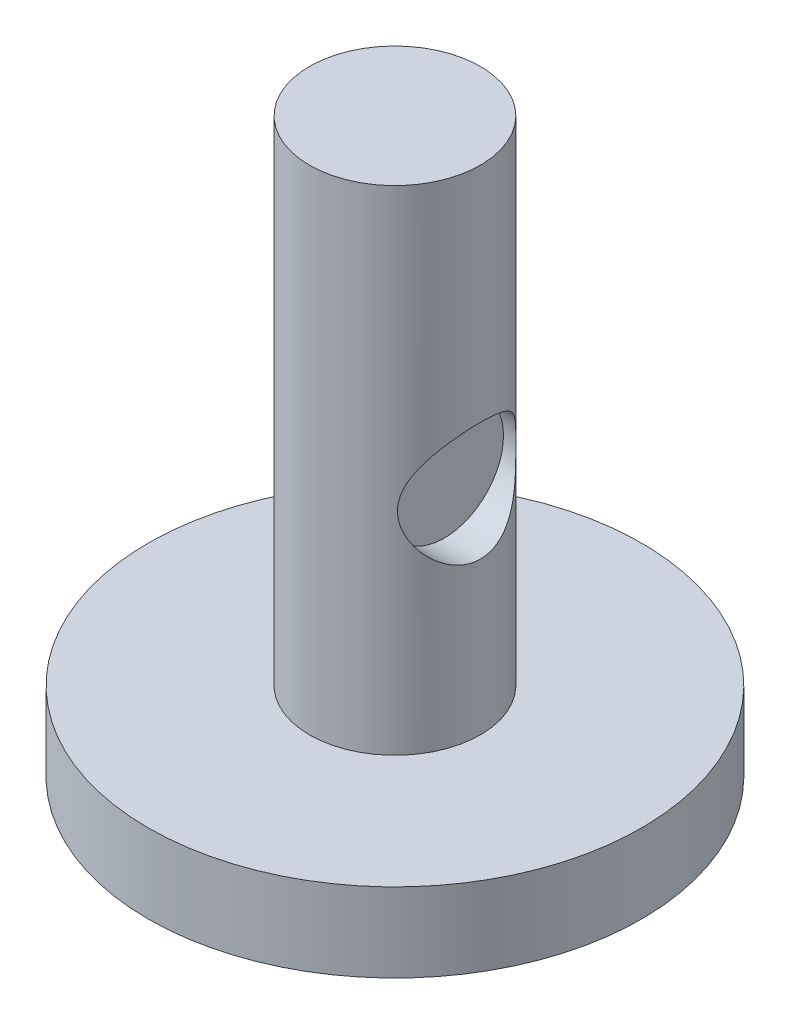
SolidWorks part; units mm, degrees
ref_plane "Front Plane" through (0, 0, 0) normal (0, 0, 1) x (1, 0, 0)
ref_plane "Top Plane" through (0, 0, 0) normal (0, 1, 0) x (1, 0, 0)
ref_plane "Right Plane" through (0, 0, 0) normal (1, 0, 0) x (0, 0, -1)
sketch "Sketch1" plane through (0, 0, 0) normal (0, 1, 0) x (1, 0, 0)
  circle A0 centre (0, 0) radius 25
  dimension "D1" = 50
extrude "Boss-Extrude1" add sketch "Sketch1" along normal blind 8
sketch "Sketch2" plane through (0, 8, 0) normal (0, 1, 0) x (1, 0, 0)
  circle A0 centre (0, 0) radius 8.665
extrude "Boss-Extrude2" add sketch "Sketch2" along normal blind 50
ref_plane "Plane1" through (20, 0, 0) normal (1, 0, 0) x (0, 0, -1)
sketch "Sketch3" plane through (20, 0, 0) normal (1, 0, 0) x (0, 0, -1)
  circle A0 centre (0, 29.4299) radius 6
  dimension "D1" = 12
extrude "Cut-Extrude1" cut sketch "Sketch3" against normal blind 15
